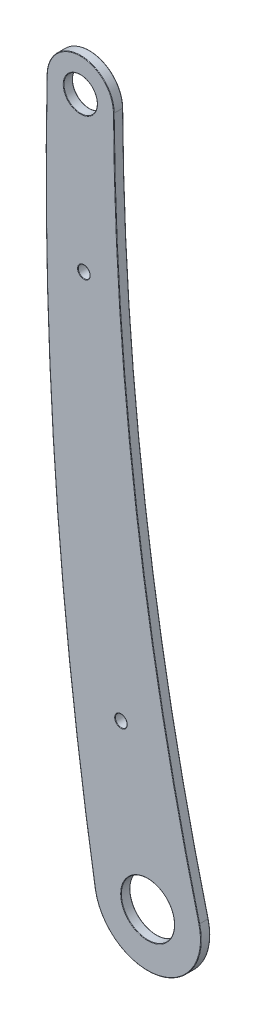
SolidWorks part; units mm, degrees
ref_plane "Front Plane" through (0, 0, 0) normal (0, 0, 1) x (1, 0, 0)
ref_plane "Top Plane" through (0, 0, 0) normal (0, 1, 0) x (1, 0, 0)
ref_plane "Right Plane" through (0, 0, 0) normal (1, 0, 0) x (0, 0, -1)
sketch "Sketch1" plane through (0, 0, 0) normal (0, 0, 1) x (1, 0, 0)
  line L0 (-20.22, 57.58) -> (-42.3309, 278.4761) construction
  line L1 (-20.22, 57.58) -> (-42.3309, 278.4761) construction
  circle A0 centre (-42.3309, 278.4761) radius 11 construction
  circle A1 centre (-42.3309, 278.4761) radius 11 construction
  circle A2 centre (-20.22, 57.58) radius 17.5 construction
  circle A3 centre (-20.22, 57.58) radius 17.5 construction
  circle A4 centre (-20.22, 57.58) radius 8.75
  circle A5 centre (-42.3309, 278.4761) radius 5.5
  arc A8 (-31.3312, 278.555) -> (-3.2662, 61.9179) centre (868.6456, 285.0094) ccw
  arc A9 (-53.328, 278.7302) -> (-37.4843, 54.7174) centre (1146.3519, 251.0131) ccw
  arc A10 (-42.3309, 278.4761) -> (-20.22, 57.58) centre (1082.6686, 279.53) ccw construction
  arc A11 (-53.328, 278.7302) -> (-31.3312, 278.555) centre (-42.3309, 278.4761) cw
  arc A12 (-37.4843, 54.7174) -> (-3.2662, 61.9179) centre (-20.22, 57.58) ccw
  circle A13 centre (-41.173, 228.4896) radius 1.95
  circle A15 centre (-28.9927, 106.8044) radius 1.95
  point P19 (-41.173, 228.4896)
  point P20 (-28.9927, 106.8044)
  dimension "D1" = 11
  dimension "D2" = 17.5
  dimension "D3" = 1200
  dimension "D4" = 1125
  dimension "D5" = 900
  dimension "D8" = 3.9
  dimension "D6" = 50
  dimension "D7" = 50
extrude "Boss-Extrude1" add sketch "Sketch1" against normal blind 3
fillet "Fillet1" radius 0.15 16 edges at (-50.658, 166.3523, -3) (-16.6164, 40.455, -3) (-23.8958, 169.3818, -3) (-42.2433, 289.4758, -3) (-11.47, 57.58, -3) (-36.8309, 278.4761, -3) (-27.0427, 106.8044, -3) (-39.223, 228.4896, -3) (-23.8958, 169.3818, 0) (-16.6164, 40.455, 0) (-50.658, 166.3523, 0) (-42.2433, 289.4758, 0) (-11.47, 57.58, 0) (-36.8309, 278.4761, 0) (-27.0427, 106.8044, 0) (-39.223, 228.4896, 0)
